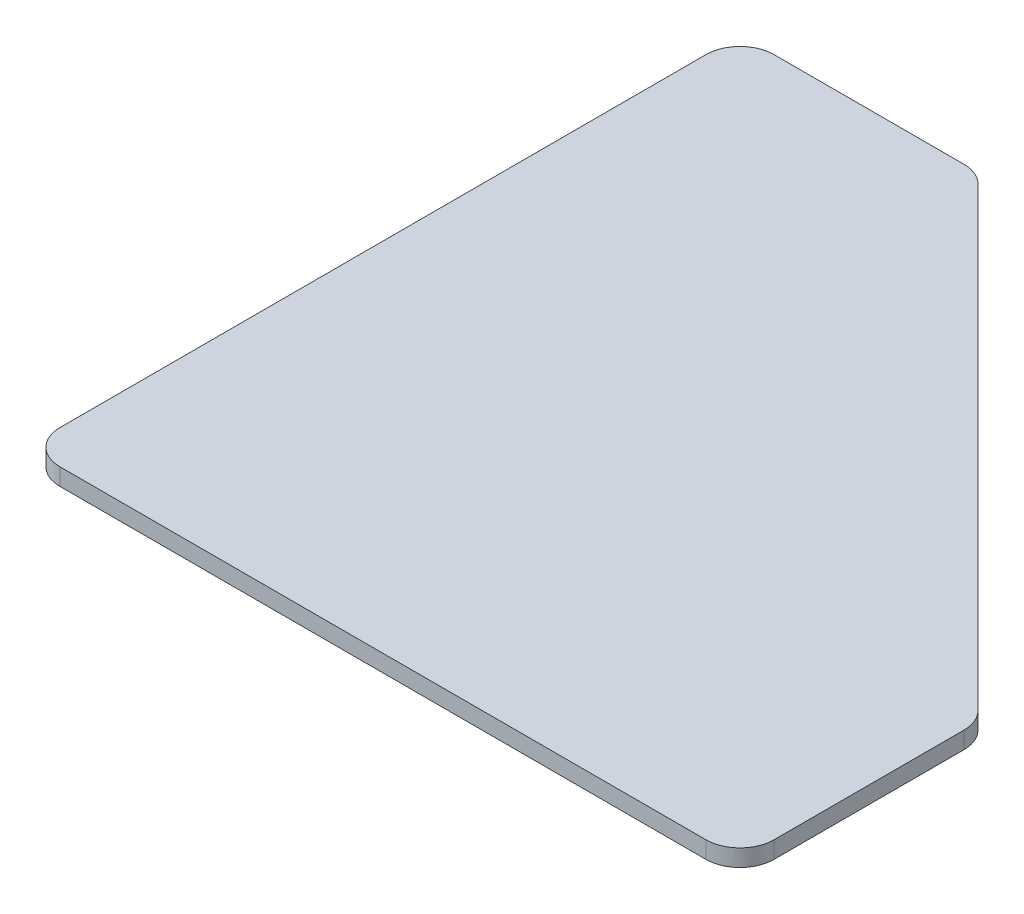
SolidWorks part; units mm, degrees
material "6061-T6 (SS)"
ref_plane "Front Plane" through (0, 0, 0) normal (0, 0, 1) x (1, 0, 0)
ref_plane "Top Plane" through (0, 0, 0) normal (0, 1, 0) x (1, 0, 0)
ref_plane "Right Plane" through (0, 0, 0) normal (1, 0, 0) x (0, 0, -1)
sketch "Sketch1" plane through (0, 0, 0) normal (0, 1, 0) x (1, 0, 0)
  line L0 (0, 0) -> (0, 133.35)
  line L1 (0, 133.35) -> (44.45, 133.35)
  line L2 (44.45, 133.35) -> (133.35, 44.45)
  line L3 (133.35, 44.45) -> (133.35, 0)
  line L4 (133.35, 0) -> (0, 0)
  dimension "D1" = 133.35
  dimension "D2" = 44.45
extrude "Boss-Extrude1" add sketch "Sketch1" along normal blind 3.175
fillet "Fillet1" radius 6.35 5 edges at (0, 1.5875, -133.35) (44.45, 1.5875, -133.35) (133.35, 1.5875, -44.45) (133.35, 1.5875, 0) (0, 1.5875, 0)
